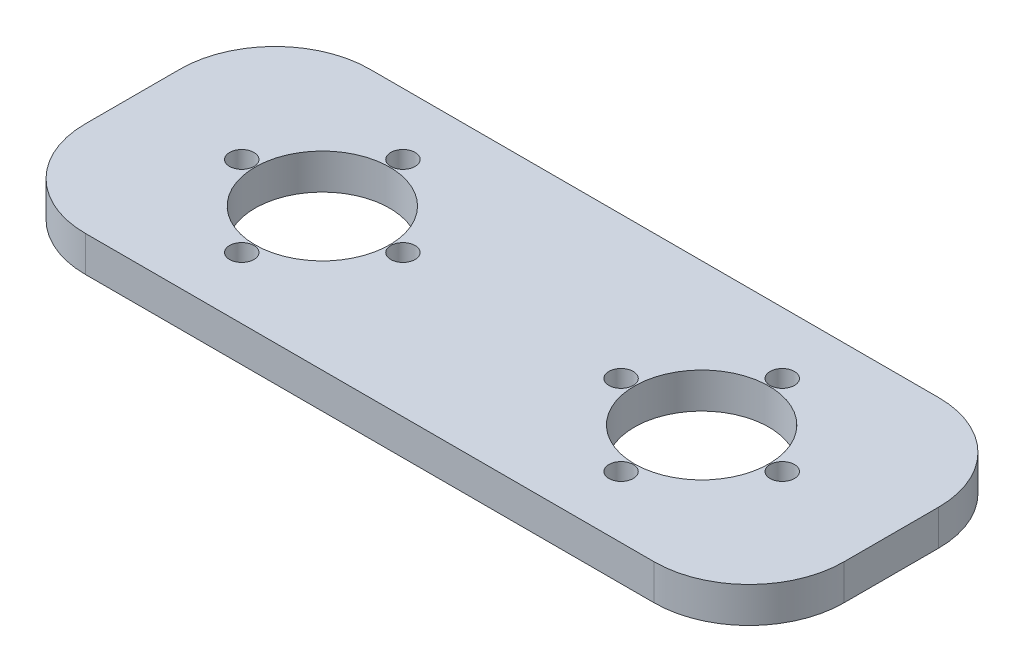
SolidWorks part; units mm, degrees
ref_plane "Front Plane" through (0, 0, 0) normal (0, 0, 1) x (1, 0, 0)
ref_plane "Top Plane" through (0, 0, 0) normal (0, 1, 0) x (1, 0, 0)
ref_plane "Right Plane" through (0, 0, 0) normal (1, 0, 0) x (0, 0, -1)
sketch "Sketch1" plane through (0, 0, 0) normal (0, 1, 0) x (1, 0, 0)
  line L0 (50.8, 38.1) -> (50.8, 0) construction
  line L1 (0, 0) -> (101.6, 0)
  line L2 (0, 0) -> (0, 38.1)
  line L3 (0, 38.1) -> (101.6, 38.1)
  line L4 (101.6, 0) -> (101.6, 38.1)
  line L5 (0, 19.05) -> (101.6, 19.05) construction
  circle A0 centre (25.4, 19.05) radius 9.017
  circle A1 centre (76.2, 19.05) radius 9.017
  dimension "D3" = 18.034
  dimension "D4" = 18.034
  dimension "D1" = 38.1
  dimension "D2" = 101.6
  dimension "D5" = 25.4
  dimension "D6" = 25.4
extrude "Boss-Extrude1" add sketch "Sketch1" along normal blind 4.7625
hole_wizard "#4 Clearance Hole1" positions "Sketch3" profile "Sketch2" hole size "#4" standard "Ansi Inch"
sketch "Sketch3" plane through (0, 4.7625, 0) normal (0, 1, 0) x (-1, 0, 0)
  line L0 (-25.4, -8.255) -> (-25.4, -29.845) construction
  line L2 (-14.605, -19.05) -> (-36.195, -19.05) construction
  line L4 (-65.405, -19.05) -> (-86.995, -19.05) construction
  line L6 (-76.2, -29.845) -> (-76.2, -8.255) construction
  circle A0 centre (-25.4, -19.05) radius 10.795
  circle A1 centre (-76.2, -19.05) radius 10.795
  point P0 (-25.4, -29.845)
  point P1 (-36.195, -19.05)
  point P3 (-25.4, -8.255)
  point P5 (-14.605, -19.05)
  point P7 (-65.405, -19.05)
  point P9 (-76.2, -29.845)
  point P11 (-86.995, -19.05)
  point P13 (-76.2, -8.255)
  dimension "D1" = 21.59
  dimension "D2" = 21.59
sketch "Sketch2" plane through (25.4, 4.7625, -29.845) normal (1, 0, 0) x (0, 0, 1)
  line L0 (0, 0) -> (0, 26.3806)
  line L1 (0, 26.3806) -> (1.6319, 25.4)
  line L2 (1.6319, 25.4) -> (1.6319, 0)
  line L5 (1.6319, 0) -> (0, 0)
  line L10 (0, 26.3806) -> (-1.6319, 25.4) construction
  line L11 (0, -6.35) -> (0, 107.95) construction
  dimension "Hole Dia." = 3.2639
  dimension "Hole Depth" = 25.4
  dimension "Drill Angle" = 118
fillet "Fillet1" radius 12.7 4 edges at (101.6, 2.3813, -38.1) (101.6, 2.3813, 0) (0, 2.3813, 0) (0, 2.3813, -38.1)
